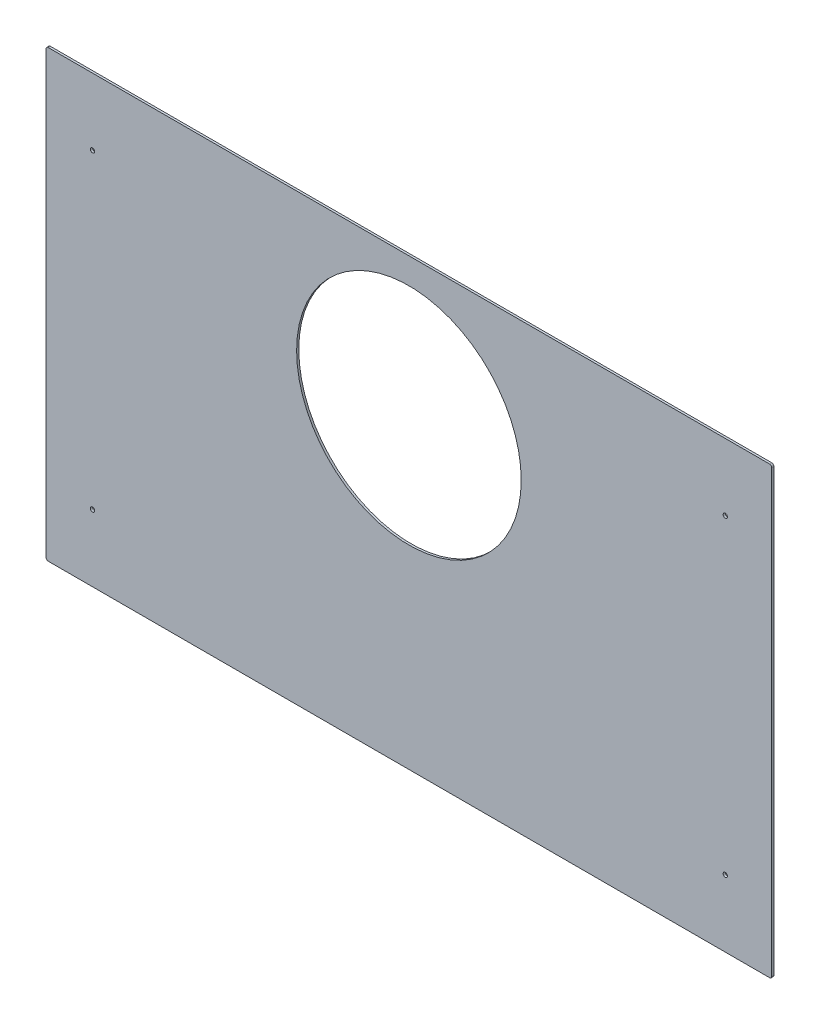
SolidWorks part; units mm, degrees
material "PC High Viscosity"
ref_plane "Front Plane" through (0, 0, 0) normal (0, 0, 1) x (1, 0, 0)
ref_plane "Top Plane" through (0, 0, 0) normal (0, 1, 0) x (1, 0, 0)
ref_plane "Right Plane" through (0, 0, 0) normal (1, 0, 0) x (0, 0, -1)
sketch "Sketch1" plane through (0, 0, 0) normal (0, 0, 1) x (1, 0, 0)
  line L1 (0, 0) -> (1066.8, 0)
  line L2 (0, 0) -> (0, 654.05)
  line L3 (0, 654.05) -> (1066.8, 654.05)
  line L4 (1066.8, 0) -> (1066.8, 654.05)
  circle A0 centre (533.4, 450.85) radius 165.1
  point P7 (533.4, 0)
  dimension "D1" = 330.2
  dimension "D2" = 654.05
  dimension "D3" = 1066.8
  dimension "D4" = 450.85
extrude "Boss-Extrude1" add sketch "Sketch1" along normal blind 3.175
hole_wizard "1/4 (0.25) Diameter Hole1" positions "Sketch2" profile "Sketch3" hole size "1/4" standard "ANSI Inch"
sketch "Sketch2" plane through (0, 0, 0) normal (0, 0, -1) x (-1, 0, 0)
  line L0 (-533.4, 654.05) -> (-533.4, 0) construction
  line L1 (-1066.8, 654.05) -> (0, 654.05) construction
  line L2 (0, 0) -> (-1066.8, 0) construction
  point P0 (-838.2, 635)
  point P2 (-533.4, 635)
  point P4 (-228.6, 635)
  dimension "D1" = 304.8
  dimension "D2" = 19.05
sketch "Sketch3" plane through (838.2, 635, 0) normal (1, 0, 0) x (0, 1, 0)
  line L0 (0, 0) -> (0, 3.175)
  line L1 (0, 3.175) -> (3.175, 3.175)
  line L2 (3.175, 3.175) -> (3.175, 0)
  line L5 (3.175, 0) -> (0, 0)
  line L11 (0, -6.35) -> (0, 107.95) construction
  dimension "Thru Hole Dia." = 6.35
  dimension "Thru Hole Depth" = 3.175
hole_wizard "1/4 (0.25) Diameter Hole2" positions "Sketch4" profile "Sketch5" hole size "1/4" standard "ANSI Inch" end condition through all
sketch "Sketch4" plane through (0, 0, 0) normal (0, 0, -1) x (-1, 0, 0)
  line L0 (-533.4, 654.05) -> (-533.4, 0) construction
  line L1 (-1066.8, 654.05) -> (0, 654.05) construction
  line L2 (0, 0) -> (-1066.8, 0) construction
  line L4 (-1066.8, 327.025) -> (0, 327.025) construction
  line L5 (-1066.8, 0) -> (-1066.8, 654.05) construction
  line L6 (0, 654.05) -> (0, 0) construction
  point P0 (-998.5375, 555.625)
  point P2 (-998.5375, 98.425)
  point P23 (-68.2625, 98.425)
  point P24 (-68.2625, 555.625)
  dimension "D1" = 228.6
  dimension "D2" = 68.2625
sketch "Sketch5" plane through (998.5375, 555.625, 0) normal (1, 0, 0) x (0, 1, 0)
  line L0 (0, 0) -> (0, 3.175)
  line L1 (0, 3.175) -> (3.175, 3.175)
  line L2 (3.175, 3.175) -> (3.175, 0)
  line L5 (3.175, 0) -> (0, 0)
  line L11 (0, -6.35) -> (0, 107.95) construction
  dimension "Thru Hole Dia." = 6.35
  dimension "Thru Hole Depth" = 3.175
fillet "Fillet1" radius 3.175 4 edges at (0, 654.05, 1.5875) (0, 0, 1.5875) (1066.8, 0, 1.5875) (1066.8, 654.05, 1.5875)
hole_wizard "1/4 Clearance Hole1" positions "Sketch6" profile "Sketch7" hole size "1/4" standard "ANSI Inch"
sketch "Sketch6" plane through (0, 0, 0) normal (0, 0, -1) x (-1, 0, 0)
  line L0 (-368.3, 450.85) -> (-698.5, 450.85) construction
  line L2 (-687.3793, 361.95) -> (-379.4207, 539.75) construction
  line L3 (-379.4207, 361.95) -> (-687.3793, 539.75) construction
  line L4 (-533.4, 273.05) -> (-533.4, 628.65) construction
  circle A0 centre (-533.4, 450.85) radius 165.1 construction
  point P0 (-533.4, 628.65)
  point P8 (-533.4, 273.05)
  point P10 (-379.4207, 539.75)
  point P12 (-687.3793, 539.75)
  point P14 (-687.3793, 361.95)
  point P16 (-379.4207, 361.95)
  point P28 (-533.4, 450.85)
  point P37 (-533.4, 450.85)
  point P39 (-533.4, 450.85)
  dimension "D1" = 60
  dimension "D2" = 12.7
sketch "Sketch7" plane through (533.4, 628.65, 0) normal (1, 0, 0) x (0, 1, 0)
  line L0 (0, 0) -> (0, 3.175)
  line L1 (0, 3.175) -> (3.3782, 3.175)
  line L2 (3.3782, 3.175) -> (3.3782, 0)
  line L5 (3.3782, 0) -> (0, 0)
  line L11 (0, -6.35) -> (0, 107.95) construction
  dimension "Thru Hole Dia." = 6.7564
  dimension "Thru Hole Depth" = 3.175
